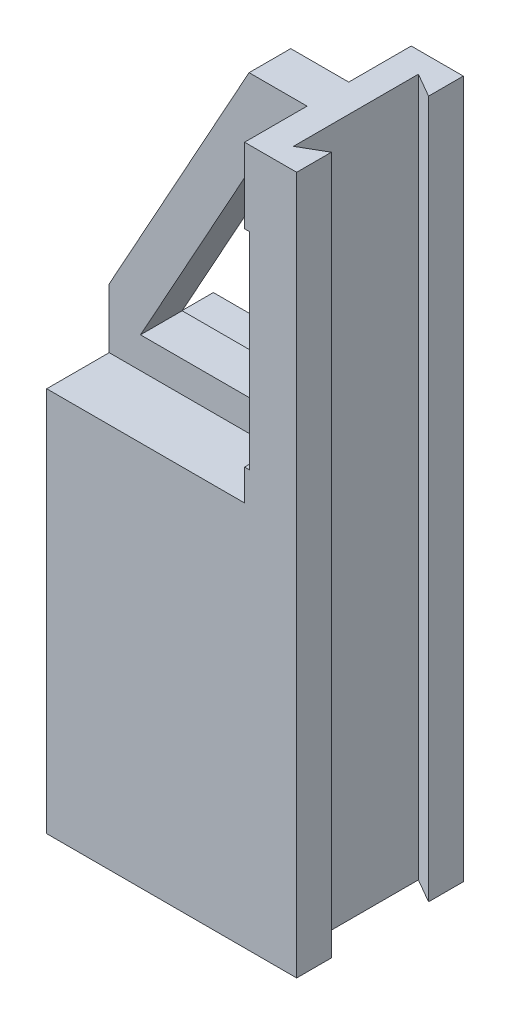
SolidWorks part; units mm, degrees
ref_plane "Спереди" through (0, 0, 0) normal (0, 0, 1) x (1, 0, 0)
ref_plane "Сверху" through (0, 0, 0) normal (0, 1, 0) x (1, 0, 0)
ref_plane "Справа" through (0, 0, 0) normal (1, 0, 0) x (0, 0, -1)
sketch "Эскиз1" plane through (0, 0, 0) normal (0, 0, 1) x (1, 0, 0)
  line L0 (0, 0) -> (120, 0)
  line L1 (120, 0) -> (120, 335)
  line L2 (120, 335) -> (67.1605, 335)
  line L3 (67.1605, 335) -> (0, 213.5954)
  line L4 (0, 213.5954) -> (0, 0)
  line L5 (15.0343, 199.9341) -> (69.8252, 298.9784)
  line L6 (69.8252, 298.9784) -> (97.3995, 298.9784)
  line L7 (97.3995, 298.9784) -> (97.3995, 199.9341)
  line L8 (97.3995, 199.9341) -> (15.0343, 199.9341)
  point P3 (0, 218.873)
  point P11 (0, 213.5954)
extrude "Бобышка-Вытянуть1" add sketch "Эскиз1" along normal blind 80
sketch "Эскиз2" plane through (0, 335, 0) normal (0, 1, 0) x (1, 0, 0)
  line L0 (120, 0) -> (67.1605, 0) construction
  line L1 (0, -30) -> (95, -30)
  line L2 (0, -30) -> (0, 0)
  line L3 (0, 0) -> (95, 0)
  line L4 (95, -30) -> (95, 0)
  line L7 (0, -40) -> (125.8899, -40) construction
  line L10 (0, -80) -> (0, 0) construction
  line L11 (95, -50) -> (95, -80)
  line L12 (0, -80) -> (95, -80)
  line L13 (0, -50) -> (0, -80)
  line L14 (0, -50) -> (95, -50)
extrude "Вырез-Вытянуть1" cut sketch "Эскиз2" against normal blind 150
sketch "Эскиз3" plane through (0, 335, 0) normal (0, 1, 0) x (1, 0, 0)
  line L0 (108.4419, -10) -> (108.4419, -70)
  line L1 (108.4419, -70) -> (120, -63.327)
  line L2 (120, -63.327) -> (120, -16.673)
  line L3 (120, -16.673) -> (108.4419, -10)
  line L4 (120, -80) -> (120, 0) construction
extrude "Вырез-Вытянуть2" cut sketch "Эскиз3" against normal through all
